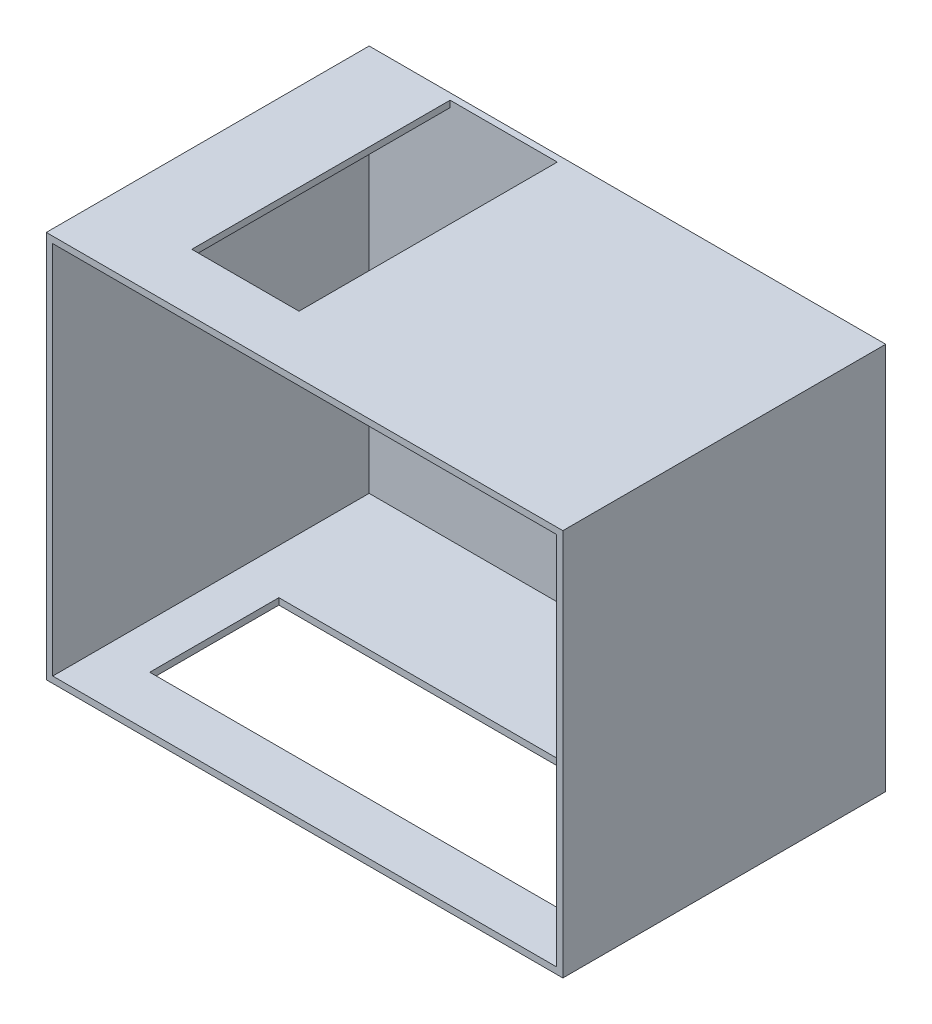
SolidWorks part; units mm, degrees
material "PVC rigide"
ref_plane "Plan de face" through (0, 0, 0) normal (0, 0, 1) x (1, 0, 0)
ref_plane "Plan de dessus" through (0, 0, 0) normal (0, 1, 0) x (1, 0, 0)
ref_plane "Plan de droite" through (0, 0, 0) normal (1, 0, 0) x (0, 0, -1)
sketch "Esquisse1" plane through (0, 0, 0) normal (0, 0, 1) x (1, 0, 0)
  line L1 (-51.8946, 2956.5623) -> (3948.1054, 2956.5623)
  line L2 (-51.8946, 2956.5623) -> (-51.8946, -43.4377)
  line L3 (-51.8946, -43.4377) -> (3948.1054, -43.4377)
  line L4 (3948.1054, 2956.5623) -> (3948.1054, -43.4377)
  dimension "D1" = 4000
  dimension "D2" = 3000
extrude "Boss.-Extru.1" add sketch "Esquisse1" along normal blind 2500
shell "Coque1" thickness 50
sketch "Esquisse2" plane through (0, -43.4377, 0) normal (0, -1, 0) x (1, 0, 0)
  line L0 (-51.8946, 2500) -> (-51.8946, 0) construction
  line L1 (348.1054, 2098.9503) -> (3548.1054, 2098.9503)
  line L2 (348.1054, 2098.9503) -> (348.1054, 1098.9503)
  line L3 (348.1054, 1098.9503) -> (3548.1054, 1098.9503)
  line L4 (3548.1054, 2098.9503) -> (3548.1054, 1098.9503)
  dimension "D1" = 3200
  dimension "D2" = 1000
  dimension "D3" = 400
extrude "Enlèv. mat.-Extru.1" cut sketch "Esquisse2" against normal up to next
sketch "Esquisse3" plane through (0, 2906.5623, 0) normal (0, -1, 0) x (1, 0, 0)
  line L0 (3898.1054, 50) -> (-1.8946, 50) construction
  line L1 (624.9306, 50) -> (1454.9306, 50)
  line L2 (624.9306, 50) -> (624.9306, 2050)
  line L3 (624.9306, 2050) -> (1454.9306, 2050)
  line L4 (1454.9306, 50) -> (1454.9306, 2050)
  dimension "D1" = 830
  dimension "D2" = 2000
extrude "Enlèv. mat.-Extru.2" cut sketch "Esquisse3" against normal up to next
